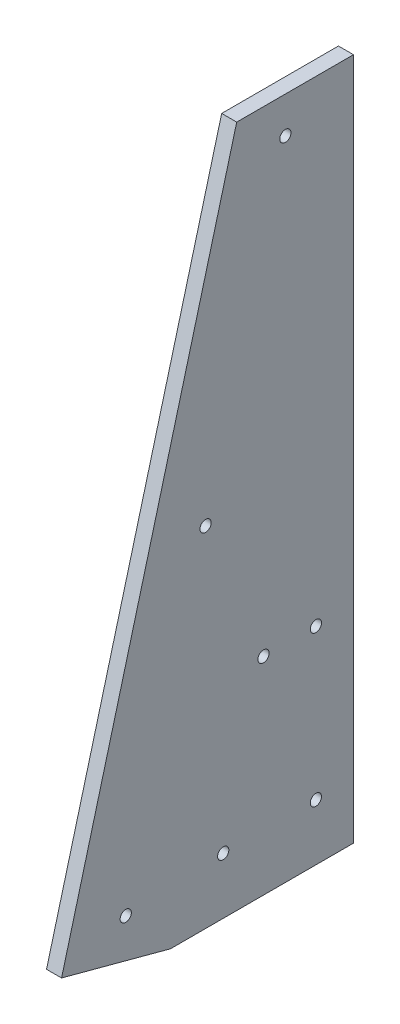
SolidWorks part; units mm, degrees
ref_plane "Front Plane" through (0, 0, 0) normal (0, 0, 1) x (1, 0, 0)
ref_plane "Top Plane" through (0, 0, 0) normal (0, 1, 0) x (1, 0, 0)
ref_plane "Right Plane" through (0, 0, 0) normal (1, 0, 0) x (0, 0, -1)
sketch "Sketch1" plane through (0, 0, 0) normal (1, 0, 0) x (0, 0, -1)
  line L0 (0, 0) -> (-36.8018, 9.861)
  line L1 (-36.8018, 9.861) -> (22.3643, 230.6716)
  line L3 (61.8083, 0) -> (0, 0)
  line L4 (22.3643, 230.6716) -> (61.8083, 230.6716)
  line L5 (61.8083, 230.6716) -> (61.8083, 0)
  line L6 (0, 0) -> (61.8083, 230.6716) construction
  dimension "D1" = 38.1
  dimension "D2" = 228.6
  dimension "D3" = 15
extrude "Boss-Extrude1" add sketch "Sketch1" along normal blind 5.08
hole_wizard "#6 Clearance Hole1" positions "Sketch3" profile "Sketch4" hole size "#6" standard "ANSI Inch" end condition through all
sketch "Sketch3" plane through (5.08, 0, 0) normal (1, 0, 0) x (0, 0, -1)
  line L0 (-18.4009, 4.9305) -> (42.0863, 230.6716)
  line L1 (-36.8018, 9.861) -> (0, 0) construction
  line L2 (61.8083, 230.6716) -> (22.3643, 230.6716) construction
  line L3 (0, 0) -> (5.1044, 19.05)
  line L4 (5.1044, 19.05) -> (61.8083, 19.05)
  line L5 (61.8083, 0) -> (61.8083, 230.6716) construction
  line L6 (22.3643, 230.6716) -> (-36.8018, 9.861) construction
  line L7 (0, 0) -> (61.8083, 0) construction
  line L8 (17.8044, 19.05) -> (31.4163, 69.85) construction
  point P8 (38.7993, 218.4044)
  point P10 (11.8427, 117.8011)
  point P12 (-15.1139, 17.1978)
  point P22 (49.1083, 19.05)
  point P24 (17.8044, 19.05)
  point P32 (31.4163, 69.85)
  point P34 (49.1083, 69.85)
  dimension "D1" = 12.7
  dimension "D2" = 12.7
  dimension "D3" = 12.7
  dimension "D4" = 12.7
  dimension "D5" = 19.05
  dimension "D6" = 69.85
sketch "Sketch4" plane through (5.08, 69.85, -49.1083) normal (0, 1, 0) x (0, 0, -1)
  line L0 (0, 0) -> (0, 5.08)
  line L1 (0, 5.08) -> (1.8986, 5.08)
  line L2 (1.8986, 5.08) -> (1.8986, 0)
  line L5 (1.8986, 0) -> (0, 0)
  line L11 (0, -6.35) -> (0, 107.95) construction
  dimension "Thru Hole Dia." = 3.7973
  dimension "Thru Hole Depth" = 5.08
